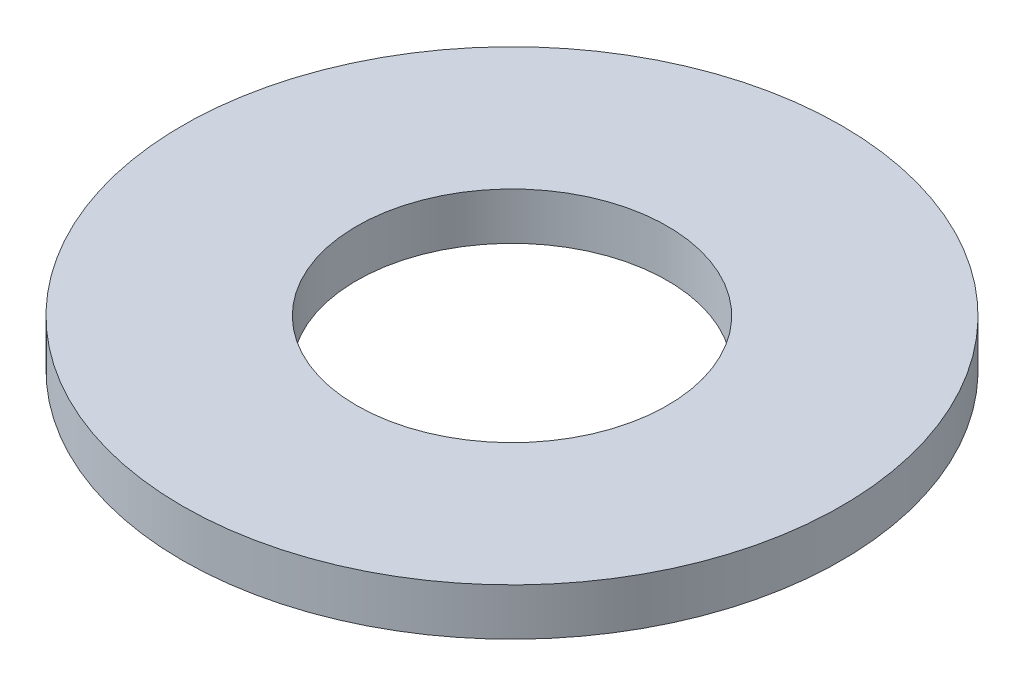
SolidWorks part; units mm, degrees
ref_plane "Front Plane" through (0, 0, 0) normal (0, 0, 1) x (1, 0, 0)
ref_plane "Top Plane" through (0, 0, 0) normal (0, 1, 0) x (1, 0, 0)
ref_plane "Right Plane" through (0, 0, 0) normal (1, 0, 0) x (0, 0, -1)
sketch "Sketch1" plane through (0, 0, 0) normal (0, 1, 0) x (1, 0, 0)
  circle A0 centre (0, 0) radius 1.65
  circle A1 centre (0, 0) radius 3.5
  dimension "D1" = 3.3
  dimension "D2" = 7
extrude "Boss-Extrude1" add sketch "Sketch1" along normal blind 0.5
